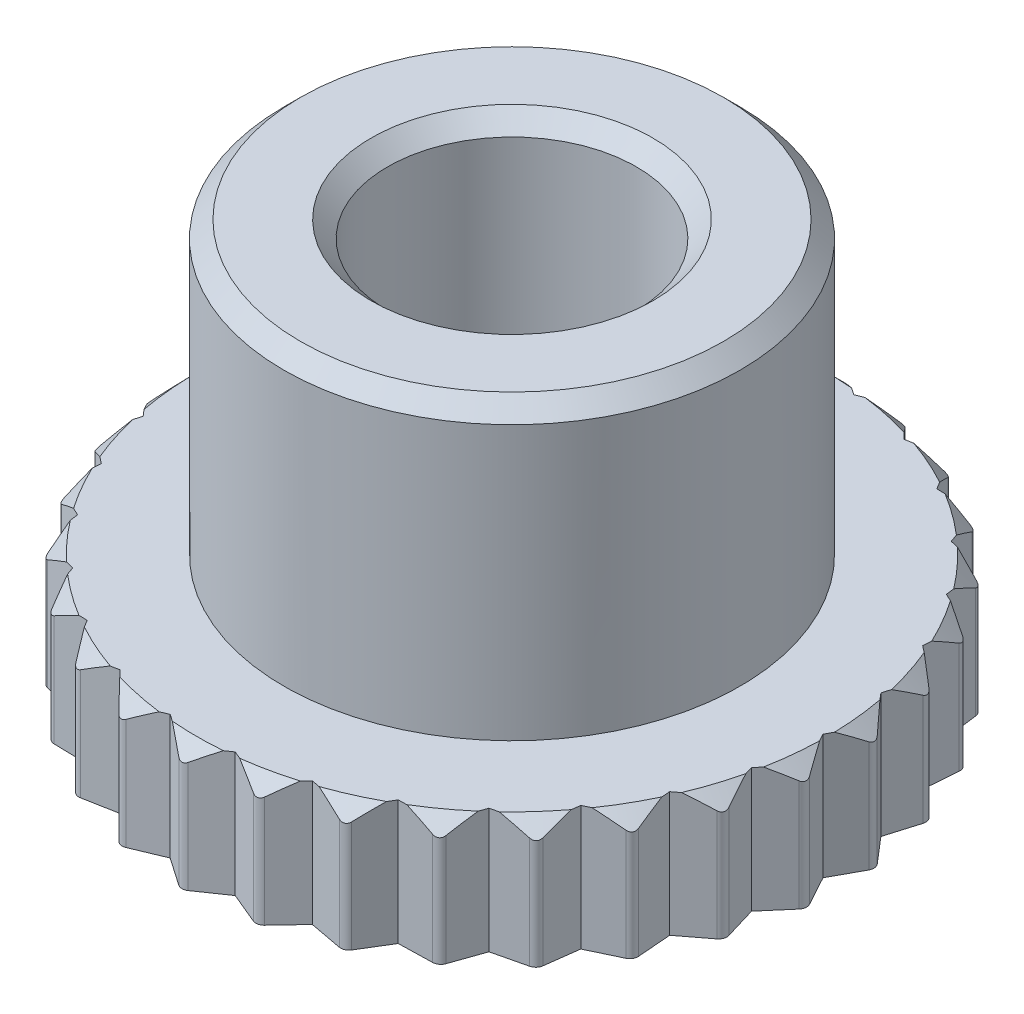
SolidWorks part; units mm, degrees
ref_plane "Ebene vorne" through (0, 0, 0) normal (0, 0, 1) x (1, 0, 0)
ref_plane "Ebene oben" through (0, 0, 0) normal (0, 1, 0) x (1, 0, 0)
ref_plane "Ebene rechts" through (0, 0, 0) normal (1, 0, 0) x (0, 0, -1)
sketch "Skizze1" plane through (0, 0, 0) normal (0, 0, 1) x (1, 0, 0)
  line L0 (0, 0) -> (8, 0)
  line L1 (8, 0) -> (8, 3)
  line L2 (8, 3) -> (5.5, 3)
  line L3 (5.5, 3) -> (5.5, 10)
  line L4 (5.5, 10) -> (0, 10)
  line L5 (0, 10) -> (0, 0)
  dimension "D1" = 3
  dimension "D2" = 10
  dimension "D3" = 5.5
  dimension "D4" = 2.5
revolve "Rotation1" add sketch "Skizze1" angle 360 about L5
sketch "Skizze9" plane through (0, 0, 0) normal (0, -1, 0) x (1, 0, 0)
  circle A0 centre (0, 0) radius 3
  circle A1 centre (0, 0) radius 8 construction
  dimension "D1" = 6
extrude "Schnitt-Linear austragen3" cut sketch "Skizze9" against normal through all
chamfer "Fase1" distance 0.4 angle 45 2 edges at (-5.5, 10, 0) (3, 10, 0)
chamfer "Fase2" distance 0.4 angle 45 1 edges at (-8, 3, 0)
sketch "Skizze8" plane through (0, 0, 0) normal (0, -1, 0) x (1, 0, 0)
  line L0 (0, 8) -> (0, -8) construction
  line L1 (-1.6633, -7.8252) -> (1.6633, 7.8252) construction
  line L2 (0, 8) -> (0.784, 7.4589)
  line L3 (0.784, 7.4589) -> (1.6633, 7.8252)
  line L4 (0, 7.5) -> (1.5593, 7.3361) construction
  line L5 (0.7797, 7.4181) -> (0.6845, 6.5122) construction
  line L6 (1.6633, 7.8252) -> (2.3176, 7.1329)
  line L7 (2.3176, 7.1329) -> (3.2539, 7.3084)
  line L8 (3.2539, 7.3084) -> (3.75, 6.4952)
  line L9 (3.75, 6.4952) -> (4.7023, 6.4721)
  line L10 (4.7023, 6.4721) -> (5.0185, 5.5736)
  line L11 (5.0185, 5.5736) -> (5.9452, 5.353)
  line L12 (5.9452, 5.353) -> (6.0676, 4.4084)
  line L13 (6.0676, 4.4084) -> (6.9282, 4)
  line L14 (6.9282, 4) -> (6.8516, 3.0505)
  line L15 (6.8516, 3.0505) -> (7.6085, 2.4721)
  line L16 (7.6085, 2.4721) -> (7.3361, 1.5593)
  line L17 (7.3361, 1.5593) -> (7.9562, 0.8362)
  line L18 (7.9562, 0.8362) -> (7.5, 0)
  line L19 (7.5, 0) -> (7.9562, -0.8362)
  line L20 (7.9562, -0.8362) -> (7.3361, -1.5593)
  line L21 (7.3361, -1.5593) -> (7.6085, -2.4721)
  line L22 (7.6085, -2.4721) -> (6.8516, -3.0505)
  line L23 (6.8516, -3.0505) -> (6.9282, -4)
  line L24 (6.9282, -4) -> (6.0676, -4.4084)
  line L25 (6.0676, -4.4084) -> (5.9452, -5.353)
  line L26 (5.9452, -5.353) -> (5.0185, -5.5736)
  line L27 (5.0185, -5.5736) -> (4.7023, -6.4721)
  line L28 (4.7023, -6.4721) -> (3.75, -6.4952)
  line L29 (3.75, -6.4952) -> (3.2539, -7.3084)
  line L30 (3.2539, -7.3084) -> (2.3176, -7.1329)
  line L31 (2.3176, -7.1329) -> (1.6633, -7.8252)
  line L32 (1.6633, -7.8252) -> (0.784, -7.4589)
  line L33 (0.784, -7.4589) -> (0, -8)
  line L34 (0, -8) -> (-0.784, -7.4589)
  line L35 (-0.784, -7.4589) -> (-1.6633, -7.8252)
  line L36 (-1.6633, -7.8252) -> (-2.3176, -7.1329)
  line L37 (-2.3176, -7.1329) -> (-3.2539, -7.3084)
  line L38 (-3.2539, -7.3084) -> (-3.75, -6.4952)
  line L39 (-3.75, -6.4952) -> (-4.7023, -6.4721)
  line L40 (-4.7023, -6.4721) -> (-5.0185, -5.5736)
  line L41 (-5.0185, -5.5736) -> (-5.9452, -5.353)
  line L42 (-5.9452, -5.353) -> (-6.0676, -4.4084)
  line L43 (-6.0676, -4.4084) -> (-6.9282, -4)
  line L44 (-6.9282, -4) -> (-6.8516, -3.0505)
  line L45 (-6.8516, -3.0505) -> (-7.6085, -2.4721)
  line L46 (-7.6085, -2.4721) -> (-7.3361, -1.5593)
  line L47 (-7.3361, -1.5593) -> (-7.9562, -0.8362)
  line L48 (-7.9562, -0.8362) -> (-7.5, 0)
  line L49 (-7.5, 0) -> (-7.9562, 0.8362)
  line L50 (-7.9562, 0.8362) -> (-7.3361, 1.5593)
  line L51 (-7.3361, 1.5593) -> (-7.6085, 2.4721)
  line L52 (-7.6085, 2.4721) -> (-6.8516, 3.0505)
  line L53 (-6.8516, 3.0505) -> (-6.9282, 4)
  line L54 (-6.9282, 4) -> (-6.0676, 4.4084)
  line L55 (-6.0676, 4.4084) -> (-5.9452, 5.353)
  line L56 (-5.9452, 5.353) -> (-5.0185, 5.5736)
  line L57 (-5.0185, 5.5736) -> (-4.7023, 6.4721)
  line L58 (-4.7023, 6.4721) -> (-3.75, 6.4952)
  line L59 (-3.75, 6.4952) -> (-3.2539, 7.3084)
  line L60 (-3.2539, 7.3084) -> (-2.3176, 7.1329)
  line L61 (-2.3176, 7.1329) -> (-1.6633, 7.8252)
  line L62 (-1.6633, 7.8252) -> (-0.784, 7.4589)
  line L63 (-0.784, 7.4589) -> (0, 8)
  circle A0 centre (0, 0) radius 8 construction
  circle A1 centre (0, 0) radius 7.5 construction
  arc A3 (1.6633, 7.8252) -> (0, 8) centre (0, 0) ccw
  arc A4 (3.2539, 7.3084) -> (1.6633, 7.8252) centre (0, 0) ccw
  arc A5 (4.7023, 6.4721) -> (3.2539, 7.3084) centre (0, 0) ccw
  arc A6 (5.9452, 5.353) -> (4.7023, 6.4721) centre (0, 0) ccw
  arc A7 (6.9282, 4) -> (5.9452, 5.353) centre (0, 0) ccw
  arc A8 (7.6085, 2.4721) -> (6.9282, 4) centre (0, 0) ccw
  arc A9 (7.9562, 0.8362) -> (7.6085, 2.4721) centre (0, 0) ccw
  arc A10 (7.9562, -0.8362) -> (7.9562, 0.8362) centre (0, 0) ccw
  arc A11 (7.6085, -2.4721) -> (7.9562, -0.8362) centre (0, 0) ccw
  arc A12 (6.9282, -4) -> (7.6085, -2.4721) centre (0, 0) ccw
  arc A13 (5.9452, -5.353) -> (6.9282, -4) centre (0, 0) ccw
  arc A14 (4.7023, -6.4721) -> (5.9452, -5.353) centre (0, 0) ccw
  arc A15 (3.2539, -7.3084) -> (4.7023, -6.4721) centre (0, 0) ccw
  arc A16 (1.6633, -7.8252) -> (3.2539, -7.3084) centre (0, 0) ccw
  arc A17 (0, -8) -> (1.6633, -7.8252) centre (0, 0) ccw
  arc A18 (-1.6633, -7.8252) -> (0, -8) centre (0, 0) ccw
  arc A19 (-3.2539, -7.3084) -> (-1.6633, -7.8252) centre (0, 0) ccw
  arc A20 (-4.7023, -6.4721) -> (-3.2539, -7.3084) centre (0, 0) ccw
  arc A21 (-5.9452, -5.353) -> (-4.7023, -6.4721) centre (0, 0) ccw
  arc A22 (-6.9282, -4) -> (-5.9452, -5.353) centre (0, 0) ccw
  arc A23 (-7.6085, -2.4721) -> (-6.9282, -4) centre (0, 0) ccw
  arc A24 (-7.9562, -0.8362) -> (-7.6085, -2.4721) centre (0, 0) ccw
  arc A25 (-7.9562, 0.8362) -> (-7.9562, -0.8362) centre (0, 0) ccw
  arc A26 (-7.6085, 2.4721) -> (-7.9562, 0.8362) centre (0, 0) ccw
  arc A27 (-6.9282, 4) -> (-7.6085, 2.4721) centre (0, 0) ccw
  arc A28 (-5.9452, 5.353) -> (-6.9282, 4) centre (0, 0) ccw
  arc A29 (-4.7023, 6.4721) -> (-5.9452, 5.353) centre (0, 0) ccw
  arc A30 (-3.2539, 7.3084) -> (-4.7023, 6.4721) centre (0, 0) ccw
  arc A31 (-1.6633, 7.8252) -> (-3.2539, 7.3084) centre (0, 0) ccw
  arc A32 (0, 8) -> (-1.6633, 7.8252) centre (0, 0) ccw
  circle A33 centre (0, 0) radius 3 construction
  point P105 (0, 0)
  circle M10 centre (0, 0) radius 8
  dimension "D2" = 0.5
  dimension "D1" = 12
  dimension "D3" = 30
extrude "Schnitt-Linear austragen1" cut sketch "Skizze8" against normal through all contours L2 L3 M10 | L6 L7 M10 | L8 L9 M10 | L10 L11 M10 | L14 L15 M10 | L16 L17 M10 | L18 L19 M10 | L22 L23 M10 | L24 L25 M10 | L28 L29 M10 | L30 L31 M10 | L32 L33 M10 | L34 L35 M10 | L36 L37 M10 | L38 L39 M10 | L40 L41 M10 | L42 L43 M10 | L44 L45 M10 | L46 L47 M10 | L48 L49 M10 | L50 L51 M10 | L52 L53 M10 | L54 L55 M10 | L56 L57 M10 | L58 L59 M10 | L60 L61 M10 | L62 L63 M10 | A7 L12 L13 | A11 L20 L21 | L26 L27 A14
fillet "Verrundung1" radius 0.2 30 edges at (0, 1.3, 8) (-1.6633, 1.3, 7.8252) (-3.2539, 1.3, 7.3084) (-4.7023, 1.3, 6.4721) (-5.9452, 1.3, 5.353) (-6.9282, 1.3, 4) (-7.6085, 1.3, 2.4721) (-7.9562, 1.3, 0.8362) (-7.9562, 1.3, -0.8362) (-7.6085, 1.3, -2.4721) (-5.9452, 1.3, -5.353) (-6.9282, 1.3, -4) (-4.7023, 1.3, -6.4721) (-3.2539, 1.3, -7.3084) (-1.6633, 1.3, -7.8252) (0, 1.3, -8) (1.6633, 1.3, -7.8252) (3.2539, 1.3, -7.3084) (4.7023, 1.3, -6.4721) (5.9452, 1.3, -5.353) (6.9282, 1.3, -4) (7.6085, 1.3, -2.4721) (7.9562, 1.3, -0.8362) (7.9562, 1.3, 0.8362) (7.6085, 1.3, 2.4721) (6.9282, 1.3, 4) (5.9452, 1.3, 5.353) (4.7023, 1.3, 6.4721) (3.2539, 1.3, 7.3084) (1.6633, 1.3, 7.8252)
